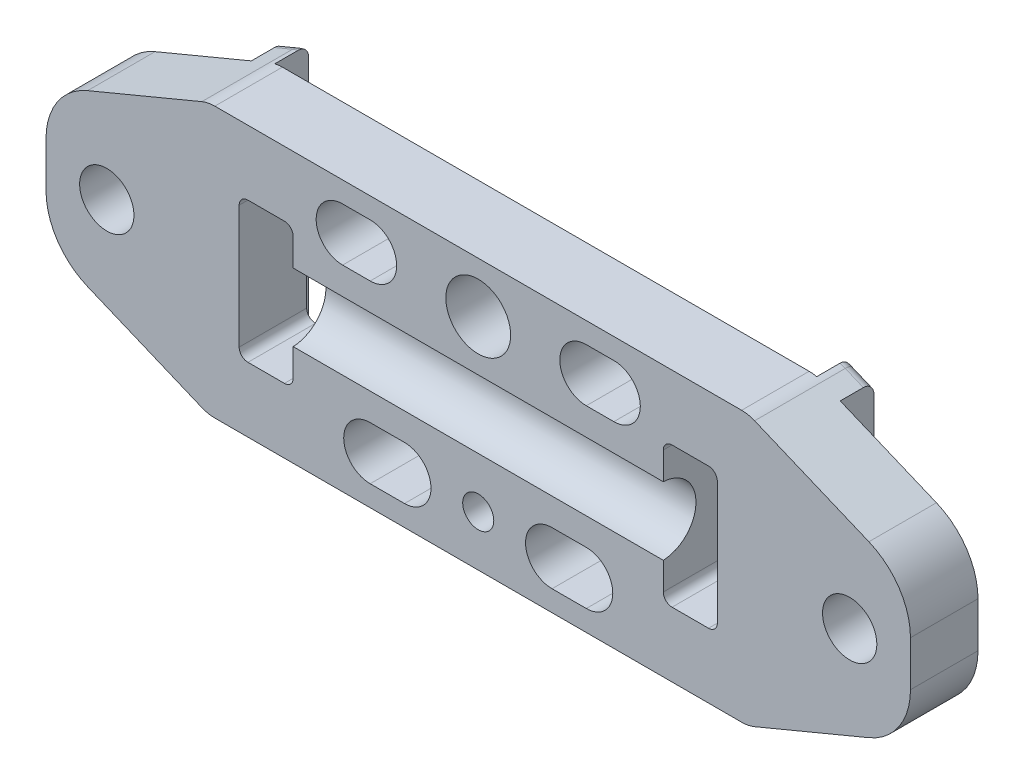
SolidWorks part; units mm, degrees
ref_plane "Front Plane" through (0, 0, 0) normal (0, 0, 1) x (1, 0, 0)
ref_plane "Top Plane" through (0, 0, 0) normal (0, 1, 0) x (1, 0, 0)
ref_plane "Right Plane" through (0, 0, 0) normal (1, 0, 0) x (0, 0, -1)
ref_plane "Plane1" through (0, 0, 0) normal (0, 0, -1) x (-1, 0, 0)
sketch "Sketch1" plane through (0, 0, 0) normal (0, 0, -1) x (-1, 0, 0)
  line L0 (-50.8, 863.6) -> (-66.04, 857.25)
  line L1 (-66.04, 857.25) -> (-66.04, 844.55)
  line L2 (-66.04, 844.55) -> (-50.8, 838.2)
  line L3 (-50.8, 838.2) -> (0, 838.2)
  line L4 (0, 838.2) -> (15.24, 844.55)
  line L5 (15.24, 844.55) -> (15.24, 857.25)
  line L6 (15.24, 857.25) -> (0, 863.6)
  line L7 (0, 863.6) -> (-50.8, 863.6)
extrude "Boss-Extrude1" add sketch "Sketch1" against normal blind 6.35
sketch "Sketch2" plane through (0, 0, 0) normal (0, 0, -1) x (-1, 0, 0)
  line L0 (-50.8762, 838.2317) -> (-66.04, 844.55)
  line L1 (-66.04, 844.55) -> (-66.04, 857.25)
  line L2 (-66.04, 857.25) -> (-50.8762, 863.5682)
  line L3 (-50.8762, 863.5682) -> (-50.8762, 838.2317)
extrude "Boss-Extrude2" add sketch "Sketch2" along normal blind 3.175
sketch "Sketch3" plane through (0, 0, 0) normal (0, 0, -1) x (-1, 0, 0)
  line L0 (0.0762, 863.5683) -> (15.24, 857.25)
  line L1 (15.24, 857.25) -> (15.24, 844.55)
  line L2 (15.24, 844.55) -> (0.0762, 838.2318)
  line L3 (0.0762, 838.2318) -> (0.0762, 863.5683)
extrude "Boss-Extrude3" add sketch "Sketch3" along normal blind 3.175
sketch "Sketch4" plane through (0, 0, -3.175) normal (0, 0, -1) x (-1, 0, 0)
  line L0 (2.286, 862.6475) -> (2.286, 839.1525)
  line L1 (2.286, 839.1525) -> (15.24, 844.55)
  line L2 (15.24, 844.55) -> (15.24, 857.25)
  line L3 (15.24, 857.25) -> (2.286, 862.6475)
extrude "Cut-Extrude1" cut sketch "Sketch4" against normal blind 3.175
sketch "Sketch5" plane through (0, 0, 0) normal (0, 0, -1) x (-1, 0, 0)
  line L0 (-8.001, 857.504) -> (-8.001, 844.296)
  line L1 (-8.001, 844.296) -> (-2.921, 844.296)
  line L2 (-2.921, 844.296) -> (-2.921, 857.504)
  line L3 (-2.921, 857.504) -> (-8.001, 857.504)
extrude "Cut-Extrude2" cut sketch "Sketch5" against normal through all
sketch "Sketch6" plane through (0, 0, 0) normal (0, 0, -1) x (-1, 0, 0)
  line L0 (-47.879, 857.504) -> (-47.879, 844.296)
  line L1 (-47.879, 844.296) -> (-42.799, 844.296)
  line L2 (-42.799, 844.296) -> (-42.799, 857.504)
  line L3 (-42.799, 857.504) -> (-47.879, 857.504)
extrude "Cut-Extrude3" cut sketch "Sketch6" against normal through all
sketch "Sketch7" plane through (8.001, 0, 0) normal (-1, 0, 0) x (0, 0, 1)
  line L0 (6.35, 847.7021) -> (6.35, 854.0979)
  arc A0 (6.35, 854.0979) -> (6.35, 847.7021) centre (6.477, 850.9) ccw
extrude "Cut-Extrude4" cut sketch "Sketch7" against normal up to next
sketch "Sketch8" plane through (0, 0, -3.175) normal (0, 0, -1) x (-1, 0, 0)
  line L0 (-53.086, 839.1525) -> (-53.086, 862.6475)
  line L1 (-53.086, 862.6475) -> (-66.04, 857.25)
  line L2 (-66.04, 857.25) -> (-66.04, 844.55)
  line L3 (-66.04, 844.55) -> (-53.086, 839.1525)
extrude "Cut-Extrude5" cut sketch "Sketch8" against normal blind 3.175
sketch "Sketch9" plane through (0, 0, 0) normal (0, 0, -1) x (-1, 0, 0)
  line L0 (-35.56, 840.1558) -> (-32.3405, 840.1558)
  line L1 (-32.3405, 845.1342) -> (-35.56, 845.1342)
  arc A0 (-35.56, 845.1342) -> (-35.56, 840.1558) centre (-35.56, 842.645) ccw
  arc A1 (-32.3405, 840.1558) -> (-32.3405, 845.1342) centre (-32.3405, 842.645) ccw
extrude "Cut-Extrude6" cut sketch "Sketch9" against normal through all
sketch "Sketch10" plane through (0, 0, 0) normal (0, 0, -1) x (-1, 0, 0)
  line L0 (-35.56, 861.6442) -> (-38.1508, 861.6442)
  line L1 (-38.1508, 856.6658) -> (-35.56, 856.6658)
  arc A0 (-35.56, 856.6658) -> (-35.56, 861.6442) centre (-35.56, 859.155) ccw
  arc A1 (-38.1508, 861.6442) -> (-38.1508, 856.6658) centre (-38.1508, 859.155) ccw
extrude "Cut-Extrude7" cut sketch "Sketch10" against normal through all
sketch "Sketch11" plane through (0, 0, 0) normal (0, 0, -1) x (-1, 0, 0)
  line L0 (-15.24, 845.1342) -> (-18.4658, 845.1342)
  line L1 (-18.4658, 840.1558) -> (-15.24, 840.1558)
  arc A0 (-15.24, 840.1558) -> (-15.24, 845.1342) centre (-15.24, 842.645) ccw
  arc A1 (-18.4658, 845.1342) -> (-18.4658, 840.1558) centre (-18.4658, 842.645) ccw
extrude "Cut-Extrude8" cut sketch "Sketch11" against normal through all
sketch "Sketch12" plane through (0, 0, 6.35) normal (0, 0, 1) x (1, 0, 0)
  line L0 (15.24, 861.6442) -> (12.6492, 861.6442)
  line L1 (12.6492, 856.6658) -> (15.24, 856.6658)
  arc A0 (15.24, 856.6658) -> (15.24, 861.6442) centre (15.24, 859.155) ccw
  arc A1 (12.6492, 861.6442) -> (12.6492, 856.6658) centre (12.6492, 859.155) ccw
extrude "Cut-Extrude9" cut sketch "Sketch12" against normal through all
sketch "Sketch13" plane through (0, 0, 0) normal (0, 0, -1) x (-1, 0, 0)
  line L0 (-26.8605, 843.0006) -> (-23.9404, 843.0006)
  line L1 (-23.9404, 843.0006) -> (-23.9404, 858.7994)
  line L2 (-26.8605, 858.8502) -> (-26.8605, 843.0006)
  arc A0 (-23.9404, 858.7994) -> (-26.8605, 858.8502) centre (-25.4, 858.8502) ccw
extrude "Cut-Extrude10" cut sketch "Sketch13" against normal blind 2.032
hole_wizard "#12 Clearance Hole1" positions "Sketch15" profile "Sketch14" hole size "#12" standard "ANSI Inch"
sketch "Sketch15" plane through (0, 0, 6.35) normal (0, 0, 1) x (1, 0, 0)
  point P0 (25.4, 858.8502)
sketch "Sketch14" plane through (25.4, 858.8502, 6.35) normal (1, 0, 0) x (0, -1, 0)
  line L0 (0, 0) -> (0, 4.953)
  line L1 (0, 4.953) -> (3.048, 4.953)
  line L2 (3.048, 4.953) -> (3.048, 0)
  line L5 (3.048, 0) -> (0, 0)
  line L10 (0, 4.953) -> (-3.048, 4.953) construction
  line L11 (0, -6.35) -> (0, 107.95) construction
  dimension "Hole Dia." = 6.096
  dimension "Hole Depth" = 4.953
  dimension "Drill Angle" = 180
hole_wizard "#3 Clearance Hole1" positions "Sketch17" profile "Sketch16" hole size "#3" standard "ANSI Inch"
sketch "Sketch17" plane through (0, 0, 6.35) normal (0, 0, 1) x (1, 0, 0)
  point P0 (25.4, 842.9498)
sketch "Sketch16" plane through (25.4, 842.9498, 6.35) normal (1, 0, 0) x (0, -1, 0)
  line L0 (0, 0) -> (0, 9.525)
  line L1 (0, 9.525) -> (1.4605, 9.525)
  line L2 (1.4605, 9.525) -> (1.4605, 0)
  line L5 (1.4605, 0) -> (0, 0)
  line L11 (0, -6.35) -> (0, 107.95) construction
  dimension "Thru Hole Dia." = 2.921
  dimension "Thru Hole Depth" = 9.525
hole_wizard "#7 (0.201) Diameter Hole1" positions "Sketch19" profile "Sketch18" hole size "#7" standard "ANSI Inch"
sketch "Sketch19" plane through (0, 0, 6.35) normal (0, 0, 1) x (1, 0, 0)
  point P0 (-9.525, 850.9)
  point P1 (60.325, 850.9)
sketch "Sketch18" plane through (-9.525, 850.9, 6.35) normal (1, 0, 0) x (0, -1, 0)
  line L0 (0, 0) -> (0, 9.525)
  line L1 (0, 9.525) -> (2.5527, 9.525)
  line L2 (2.5527, 9.525) -> (2.5527, 0)
  line L5 (2.5527, 0) -> (0, 0)
  line L11 (0, -6.35) -> (0, 107.95) construction
  dimension "Thru Hole Dia." = 5.1054
  dimension "Thru Hole Depth" = 9.525
fillet "Fillet1" radius 3.175 4 edges at (0, 838.2, 3.175) (50.8, 838.2, 3.175) (50.8, 863.6, 3.175) (0, 863.6, 3.175)
fillet "Fillet2" radius 0.8255 8 edges at (42.799, 857.504, 3.175) (2.921, 844.296, 3.175) (2.921, 857.504, 3.175) (47.879, 857.504, 3.175) (42.799, 844.296, 3.175) (8.001, 857.504, 3.175) (8.001, 844.296, 3.175) (47.879, 844.296, 3.175)
fillet "Fillet3" radius 1 8 edges at (52.2361, 863.0016, -3.175) (51.1346, 863.4483, -3.175) (-1.4361, 838.7984, -3.175) (-0.3346, 838.3517, -3.175) (51.1346, 838.3517, -3.175) (52.2361, 838.7984, -3.175) (-1.4361, 863.0016, -3.175) (-0.3346, 863.4483, -3.175)
fillet "Fillet4" radius 6.35 4 edges at (66.04, 844.55, 3.175) (66.04, 857.25, 3.175) (-15.24, 844.55, 3.175) (-15.24, 857.25, 3.175)
